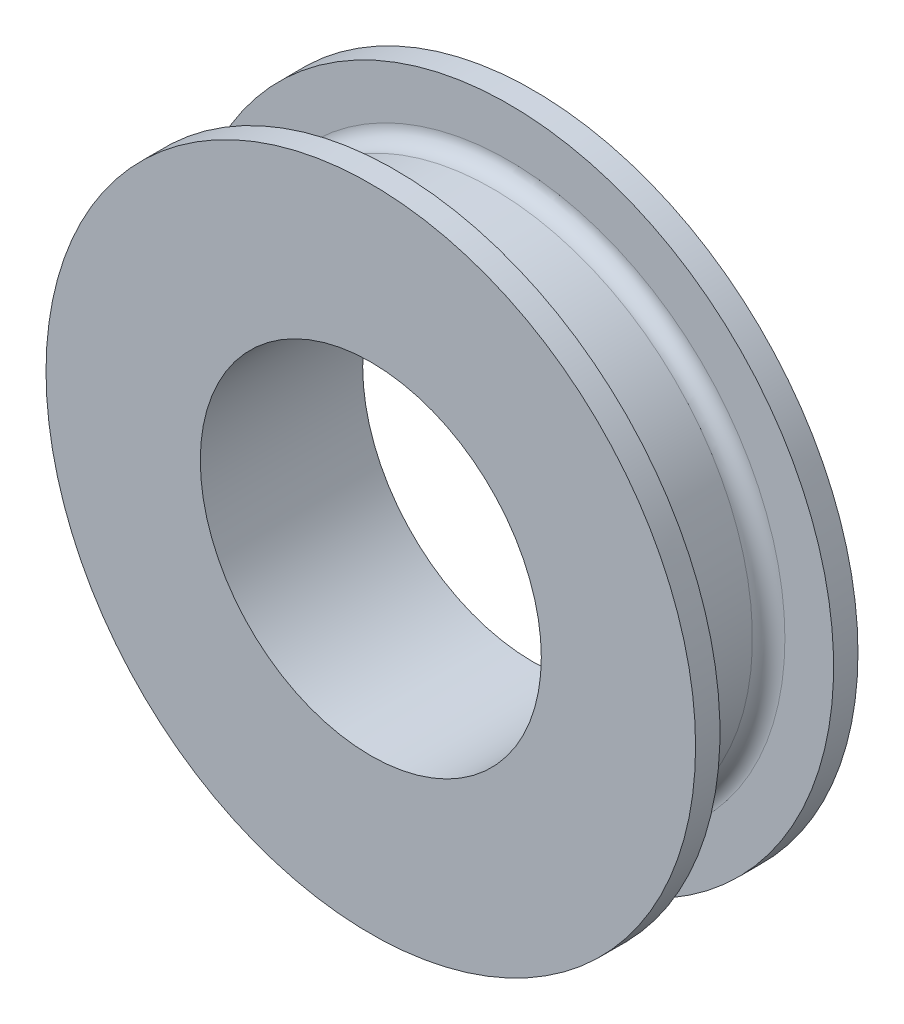
SolidWorks part; units mm, degrees
ref_plane "前视基准面" through (0, 0, 0) normal (0, 0, 1) x (1, 0, 0)
ref_plane "上视基准面" through (0, 0, 0) normal (0, 1, 0) x (1, 0, 0)
ref_plane "右视基准面" through (0, 0, 0) normal (1, 0, 0) x (0, 0, -1)
sketch "草图1" plane through (0, 0, 0) normal (0, 0, 1) x (1, 0, 0)
  line L1 (0, 25) -> (0, -25) construction
  line L2 (0, 0) -> (-25, 0) construction
  line L3 (0, 0) -> (25, 0) construction
  circle A0 centre (0, 0) radius 21
  circle A1 centre (0, 0) radius 30
  circle A2 centre (0, 0) radius 40
extrude "凸台-拉伸1" add sketch "草图1" along normal mid plane 20 contours A1 A0 | A2 A1
sketch "草图2" plane through (0, 0, 0) normal (1, 0, 0) x (0, 0, -1)
  line L4 (-7, 40) -> (-7, 34)
  line L6 (-5, 32) -> (5, 32)
  line L7 (7, 34) -> (7, 40)
  line L8 (0, 0) -> (-10, 0) construction
  line L9 (-7, 40) -> (7, 40)
  arc A0 (5, 32) -> (7, 34) centre (5, 34) ccw
  arc A1 (-5, 32) -> (-7, 34) centre (-5, 34) cw
  point P0 (0, 40)
revolve "切除-旋转1" cut sketch "草图2" angle 360 about L8
